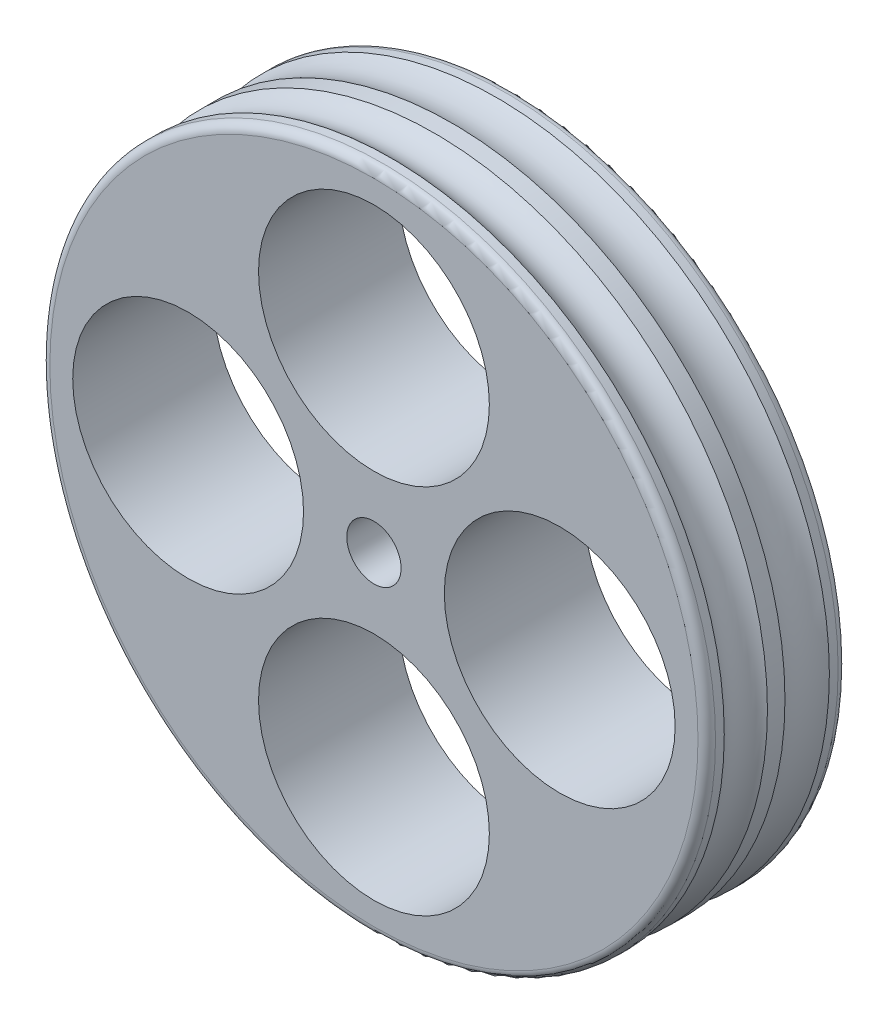
SolidWorks part; units mm, degrees
ref_plane "Front Plane" through (0, 0, 0) normal (0, 0, 1) x (1, 0, 0)
ref_plane "Top Plane" through (0, 0, 0) normal (0, 1, 0) x (1, 0, 0)
ref_plane "Right Plane" through (0, 0, 0) normal (1, 0, 0) x (0, 0, -1)
sketch "Sketch1" plane through (0, 0, 0) normal (0, 0, 1) x (1, 0, 0)
  circle A0 centre (0, 0) radius 19
  dimension "D1" = 38
extrude "Boss-Extrude1" add sketch "Sketch1" along normal blind 8
ref_axis "Axis1" through (0, 0, 8.4) along (0, 0, -1)
sketch "Sketch2" plane through (0, 0, 0) normal (1, 0, 0) x (0, 0, -1)
  line L0 (0, 19) -> (-8, 19) construction
  line L1 (-8, 19) -> (-8, -19) construction
  line L2 (0, 20.9) -> (0, -20.9) construction
  line L3 (-8.4, 0) -> (0.4, 0) construction
  line L4 (-7, 19) -> (-4.5352, 19)
  line L5 (-3.5352, 19) -> (-1, 19)
  arc A0 (-1, 19) -> (-3.5352, 19) centre (-2.2676, 21.528) cw
  arc A1 (-4.5352, 19) -> (-7, 19) centre (-5.7676, 20.2688) cw
  point P12 (-5.7676, 18.5)
  point P17 (-2.2676, 18.7)
  dimension "D1" = 1
  dimension "D2" = 1
  dimension "D3" = 1
  dimension "D4" = 18.5
  dimension "D5" = 18.7
revolve "Cut-Revolve1" cut sketch "Sketch2" angle 360 about axis through (0, 0, 8.4) along (0, 0, -1)
fillet "Fillet1" radius 0.5 2 edges at (19, 0, 0) (19, 0, 8)
sketch "Sketch3" plane through (0, 0, 8) normal (0, 0, 1) x (1, 0, 0)
  circle A0 centre (0, 0) radius 1.55
  dimension "D1" = 3.1
extrude "Cut-Extrude1" cut sketch "Sketch3" against normal blind 8
sketch "Sketch4" plane through (0, 0, 8) normal (0, 0, 1) x (1, 0, 0)
  line L0 (0, -4.4) -> (0, 4.4) construction
  circle A0 centre (0, 10.6065) radius 6.589
  point P4 (0, 10.6731)
  point P5 (0, 10.6065)
extrude "Cut-Extrude2" cut sketch "Sketch4" against normal blind 8
pattern_circular "CirPattern1" count 4 over 360 about axis through (0, 0, 0) along (0, 0, 1) of "Cut-Extrude2"
